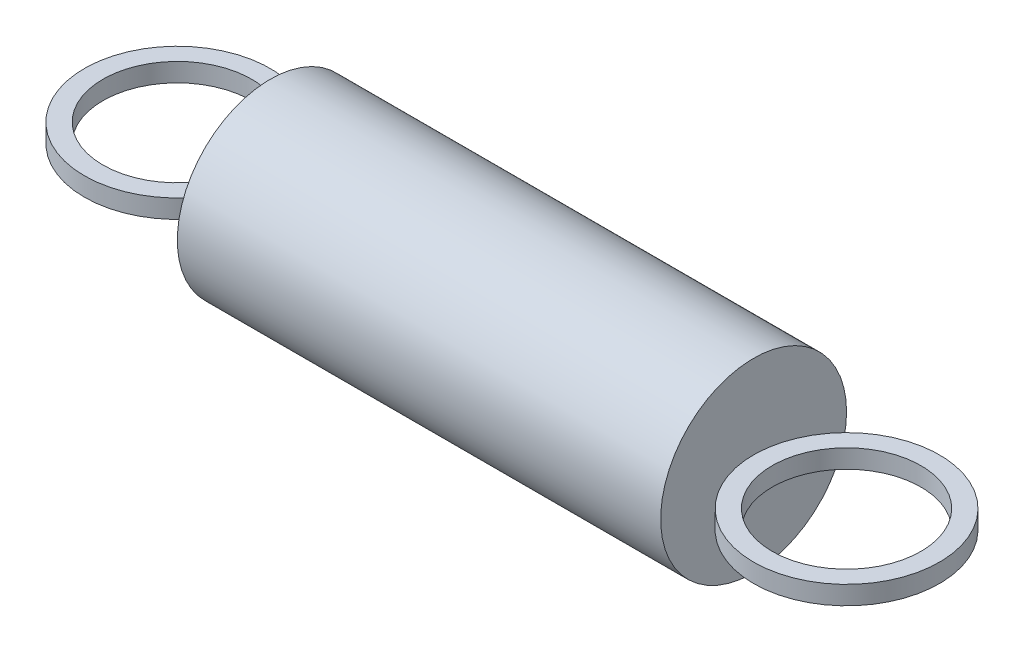
SolidWorks part; units mm, degrees
ref_plane "Front Plane" through (0, 0, 0) normal (0, 0, 1) x (1, 0, 0)
ref_plane "Top Plane" through (0, 0, 0) normal (0, 1, 0) x (1, 0, 0)
ref_plane "Right Plane" through (0, 0, 0) normal (1, 0, 0) x (0, 0, -1)
sketch "Sketch1" plane through (0, 0, 0) normal (1, 0, 0) x (0, 0, -1)
  circle A0 centre (0, 0) radius 3.9688
  dimension "D1" = 7.9375
extrude "Boss-Extrude1" add sketch "Sketch1" along normal blind 20.6375
sketch "Sketch3" plane through (0, 0, 0) normal (0, 1, 0) x (1, 0, 0)
  line L0 (20.6375, -3.9688) -> (20.6375, 3.9688) construction
  circle A0 centre (-3.9688, 0) radius 3.9688
  circle A1 centre (24.6062, 0) radius 3.9687
  circle A2 centre (-3.9688, 0) radius 3.175
  circle A3 centre (24.6062, 0) radius 3.175
  dimension "D1" = 7.9375
  dimension "D2" = 0.7937
extrude "Boss-Extrude2" add sketch "Sketch3" along normal mid plane 0.7937 separate body
ref_plane "Plane1" through (0, 0, 3.9688) normal (0, 0, 1) x (1, 0, 0)
